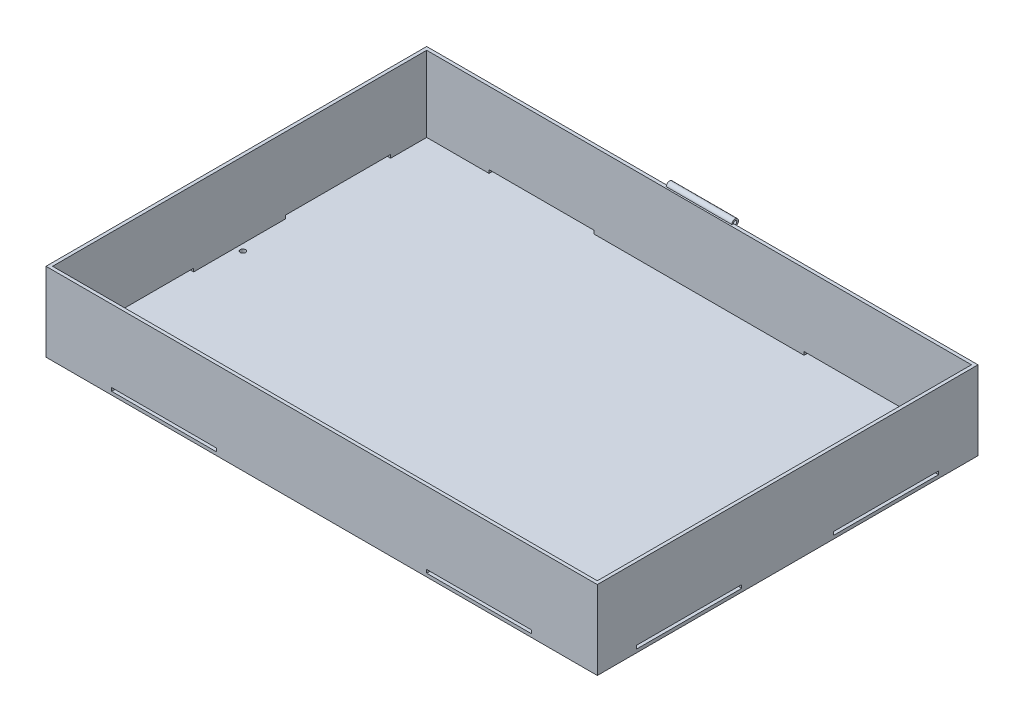
SolidWorks part; units mm, degrees
ref_plane "Front Plane" through (0, 0, 0) normal (0, 0, 1) x (1, 0, 0)
ref_plane "Top Plane" through (0, 0, 0) normal (0, 1, 0) x (1, 0, 0)
ref_plane "Right Plane" through (0, 0, 0) normal (1, 0, 0) x (0, 0, -1)
sketch "Sketch1" plane through (0, 0, 0) normal (0, 1, 0) x (1, 0, 0)
  line L0 (0, 28.431) -> (0, -34.6955) construction
  line L1 (0, -34.6955) -> (0, 0) construction
  line L2 (-89.7906, 0) -> (95.8944, 0) construction
  line L4 (533.4, 368.3) -> (-533.4, 368.3)
  line L5 (533.4, 368.3) -> (533.4, -368.3)
  line L6 (533.4, -368.3) -> (-533.4, -368.3)
  line L7 (-533.4, 368.3) -> (-533.4, -368.3)
  line L8 (533.4, 368.3) -> (-533.4, -368.3) construction
  line L9 (533.4, -368.3) -> (-533.4, 368.3) construction
  dimension "D1" = 736.6
  dimension "D2" = 1066.8
extrude "Boss-Extrude1" add sketch "Sketch1" along normal blind 152.4 contours L4 L7 L6 L5
shell "Shell1" thickness 6.35
sketch "Sketch2" plane through (0, 6.35, 0) normal (0, 1, 0) x (1, 0, 0)
  line L0 (0, 168.8818) -> (0, -121.2675) construction
  line L1 (527.05, 361.95) -> (-527.05, 361.95) construction
  circle A0 centre (-514.35, -6.35) radius 5.08
  circle A1 centre (514.35, -6.35) radius 5.08
  point P5 (0, 0)
  dimension "D1" = 10.16
  dimension "D3" = 368.3
  dimension "D2" = 514.35
extrude "Cut-Extrude1" cut sketch "Sketch2" against normal through all
sketch "Sketch3" plane through (0, 0, 368.3) normal (0, 0, 1) x (1, 0, 0)
  line L0 (533.4, 0) -> (-533.4, 0) construction
  line L1 (-406.4, 6.35) -> (-203.2, 6.35)
  line L2 (-406.4, 6.35) -> (-406.4, 12.7)
  line L3 (-406.4, 12.7) -> (-203.2, 12.7)
  line L4 (-203.2, 6.35) -> (-203.2, 12.7)
  line L5 (0, 138.2826) -> (0, -118.4912) construction
  line L6 (-533.4, 152.4) -> (-533.4, 0) construction
  line L7 (406.4, 6.35) -> (406.4, 12.7)
  line L8 (203.2, 6.35) -> (203.2, 12.7)
  line L9 (406.4, 6.35) -> (203.2, 6.35)
  line L10 (406.4, 12.7) -> (203.2, 12.7)
  point P4 (0, 0)
  point P5 (0, 0)
  point P15 (0, 0)
  dimension "D1" = 203.2
  dimension "D2" = 6.35
  dimension "D3" = 127
  dimension "D4" = 6.35
extrude "Cut-Extrude3" cut sketch "Sketch3" against normal through all
sketch "Sketch4" plane through (-533.4, 0, 0) normal (-1, 0, 0) x (0, 0, 1)
  line L1 (-292.1, 6.35) -> (-88.9, 6.35)
  line L2 (-292.1, 6.35) -> (-292.1, 12.7)
  line L3 (-292.1, 12.7) -> (-88.9, 12.7)
  line L4 (-88.9, 6.35) -> (-88.9, 12.7)
  line L5 (-368.3, 0) -> (368.3, 0) construction
  line L6 (-368.3, 152.4) -> (-368.3, 0) construction
  line L7 (0, 140.1456) -> (0, -76.9932) construction
  line L8 (88.9, 6.35) -> (88.9, 12.7)
  line L9 (292.1, 12.7) -> (88.9, 12.7)
  line L10 (292.1, 6.35) -> (88.9, 6.35)
  line L11 (292.1, 6.35) -> (292.1, 12.7)
  dimension "D1" = 6.35
  dimension "D2" = 203.2
  dimension "D3" = 6.35
  dimension "D4" = 76.2
extrude "Cut-Extrude4" cut sketch "Sketch4" against normal through all
ref_plane "Plane1" through (-3.175, 0, 0) normal (-1, 0, 0) x (0, 0, 1)
sketch "Sketch6" plane through (-3.175, 0, 0) normal (-1, 0, 0) x (0, 0, 1)
  line L1 (-368.3, 142.24) -> (-361.95, 142.24) construction
  line L2 (-368.3, 152.4) -> (-368.3, 0) construction
  line L3 (-368.3, 152.4) -> (368.3, 152.4) construction
  arc A0 (-365.063, 152.4) -> (-377.887, 152.4) centre (-371.475, 152.4) ccw
  arc A1 (-377.887, 152.4) -> (-365.063, 152.4) centre (-371.475, 152.4) ccw
  circle A2 centre (-371.475, 152.4) radius 3.175
  point P12 (0, 0)
  point P13 (0, 0)
  dimension "D1" = 6.412
  dimension "D2" = 6.35
  dimension "D6" = 152.4
  dimension "D3" = 6.35
  dimension "D4" = 9.525
  dimension "D5" = 10.16
extrude "Boss-Extrude3" add sketch "Sketch6" along normal mid plane 127
